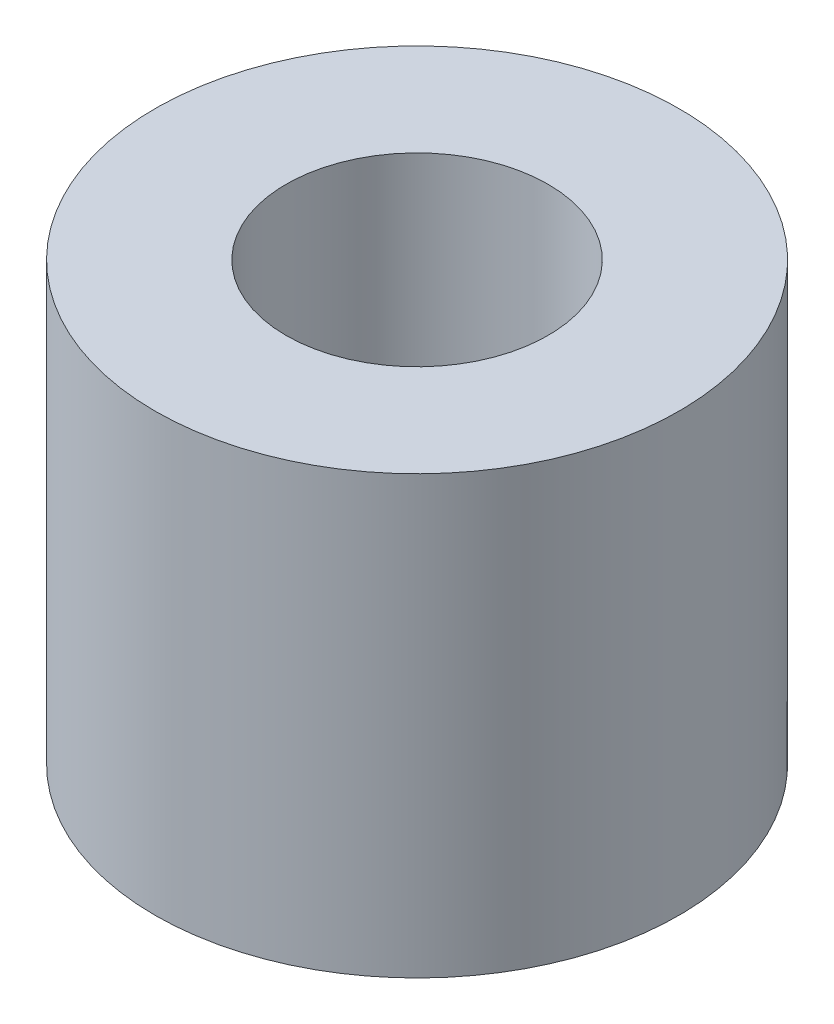
SolidWorks part; units mm, degrees
ref_plane "Front Plane" through (0, 0, 0) normal (0, 0, 1) x (1, 0, 0)
ref_plane "Top Plane" through (0, 0, 0) normal (0, 1, 0) x (1, 0, 0)
ref_plane "Right Plane" through (0, 0, 0) normal (1, 0, 0) x (0, 0, -1)
sketch "Sketch1" plane through (0, 0, 0) normal (0, 1, 0) x (1, 0, 0)
  circle A0 centre (0, 0) radius 3
  circle A1 centre (0, 0) radius 1.5
  dimension "D1" = 3
  dimension "D2" = 6
extrude "Boss-Extrude1" add sketch "Sketch1" along normal blind 5
